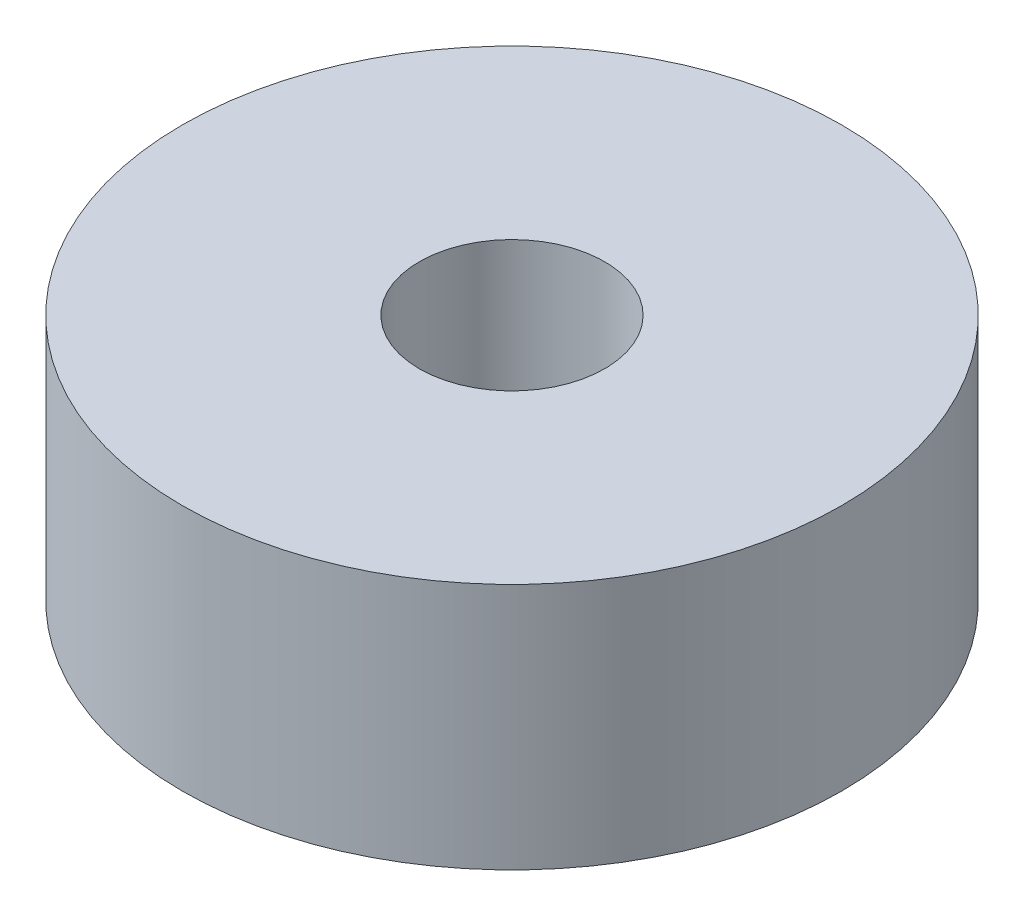
SolidWorks part; units mm, degrees
ref_plane "Front Plane" through (0, 0, 0) normal (0, 0, 1) x (1, 0, 0)
ref_plane "Top Plane" through (0, 0, 0) normal (0, 1, 0) x (1, 0, 0)
ref_plane "Right Plane" through (0, 0, 0) normal (1, 0, 0) x (0, 0, -1)
sketch "Sketch1" plane through (0, 0, 0) normal (0, 1, 0) x (1, 0, 0)
  circle A0 centre (0, 0) radius 8
  circle A1 centre (0, 0) radius 2.25
  dimension "D1" = 4.5
  dimension "D2" = 16
extrude "Boss-Extrude1" add sketch "Sketch1" along normal blind 6
